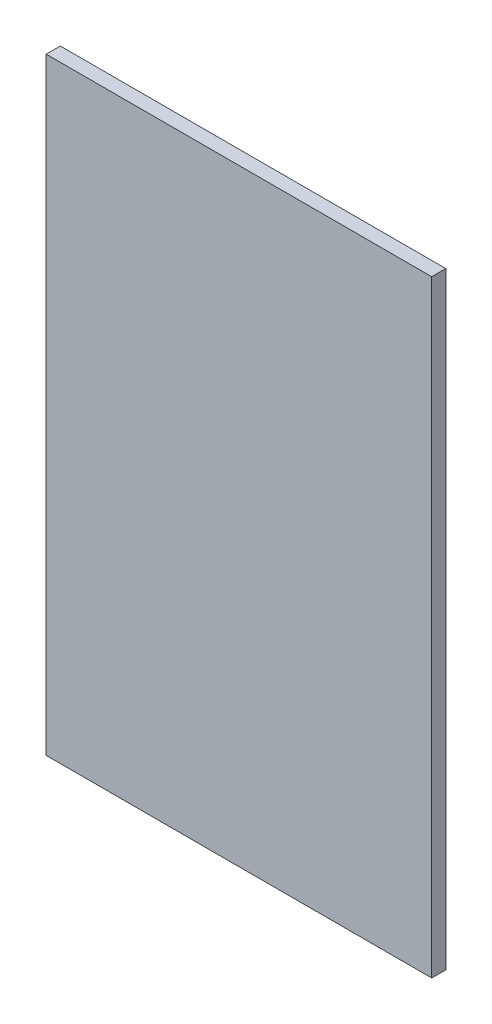
SolidWorks part; units mm, degrees
ref_plane "Front Plane" through (0, 0, 0) normal (0, 0, 1) x (1, 0, 0)
ref_plane "Top Plane" through (0, 0, 0) normal (0, 1, 0) x (1, 0, 0)
ref_plane "Right Plane" through (0, 0, 0) normal (1, 0, 0) x (0, 0, -1)
sketch "Sketch2" plane through (0, 0, 0) normal (0, 0, 1) x (1, 0, 0)
  line L2 (64.0488, 77.3656) -> (146.0488, 77.3656)
  line L3 (64.0488, 77.3656) -> (64.0488, -51.8049)
  line L4 (64.0488, -51.8049) -> (146.0488, -51.8049)
  line L5 (146.0488, 77.3656) -> (146.0488, -51.8049)
  dimension "D1" = 153
  dimension "D2" = 82
extrude "Boss-Extrude1" add sketch "Sketch2" along normal blind 3
